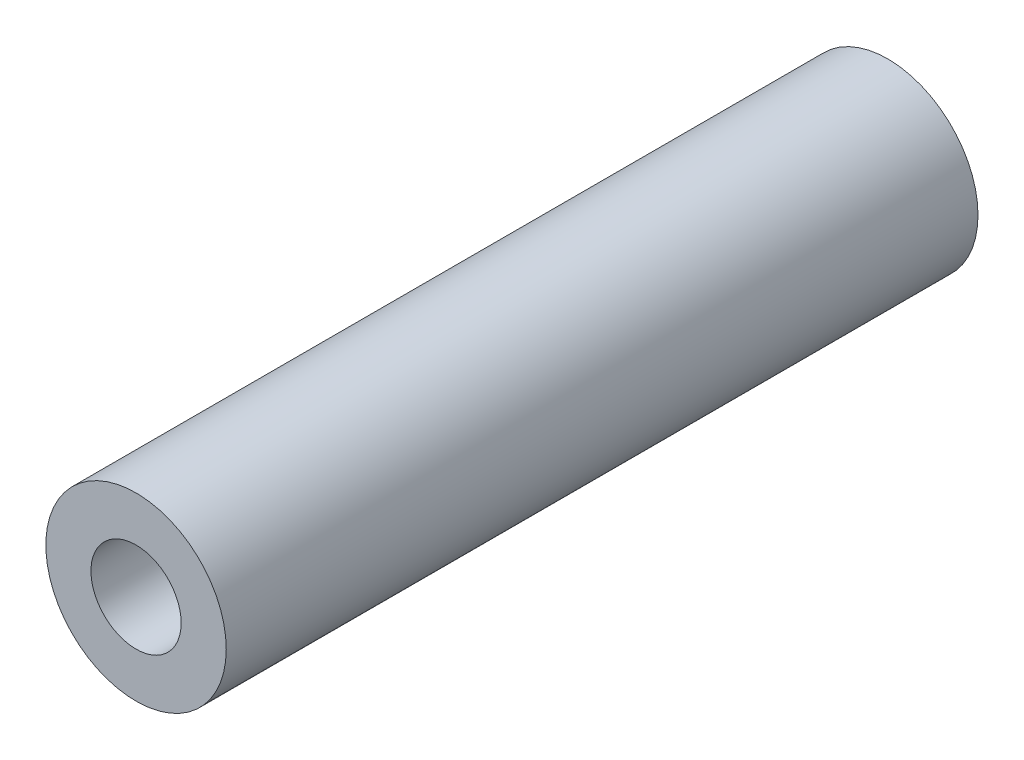
SolidWorks part; units mm, degrees
material "Nylon 6/10"
ref_plane "Front Plane" through (0, 0, 0) normal (0, 0, 1) x (1, 0, 0)
ref_plane "Top Plane" through (0, 0, 0) normal (0, 1, 0) x (1, 0, 0)
ref_plane "Right Plane" through (0, 0, 0) normal (1, 0, 0) x (0, 0, -1)
sketch "Sketch1" plane through (0, 0, 0) normal (0, 0, 1) x (1, 0, 0)
  circle A0 centre (0, 0) radius 1.5
  circle A1 centre (0, 0) radius 3
  dimension "D1" = 6
  dimension "D2" = 3
extrude "Boss-Extrude1" add sketch "Sketch1" along normal blind 25
